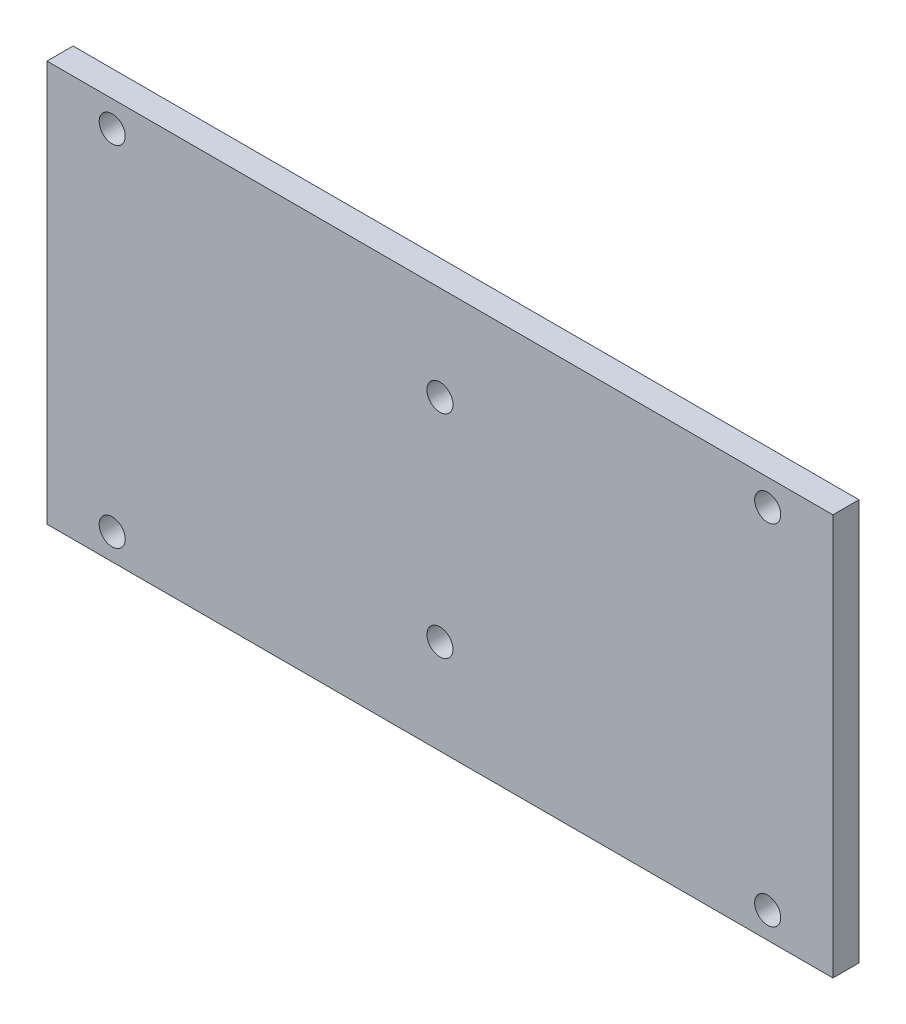
SolidWorks part; units mm, degrees
ref_plane "Alzado" through (0, 0, 0) normal (0, 0, 1) x (1, 0, 0)
ref_plane "Planta" through (0, 0, 0) normal (0, 1, 0) x (1, 0, 0)
ref_plane "Vista lateral" through (0, 0, 0) normal (1, 0, 0) x (0, 0, -1)
sketch "Croquis1" plane through (0, 0, 0) normal (0, 0, 1) x (1, 0, 0)
  line L0 (0, 41.8382) -> (0, -43.7054) construction
  line L1 (60.25, -30.75) -> (-60.25, -30.75)
  line L2 (60.25, -30.75) -> (60.25, 30.75)
  line L3 (60.25, 30.75) -> (-60.25, 30.75)
  line L4 (-60.25, -30.75) -> (-60.25, 30.75)
  line L5 (60.25, -30.75) -> (-60.25, 30.75) construction
  line L6 (60.25, 30.75) -> (-60.25, -30.75) construction
  circle A0 centre (-50.25, 26.75) radius 2
  circle A1 centre (-50.25, -26.75) radius 2
  circle A2 centre (50.25, -26.75) radius 2
  circle A3 centre (50.25, 26.75) radius 2
  circle A4 centre (0, 16.25) radius 2
  circle A5 centre (0, -16.25) radius 2
  point P0 (0, 0)
  dimension "D3" = 4
  dimension "D6" = 4
  dimension "D8" = 4
  dimension "D9" = 4
  dimension "D1" = 120.5
  dimension "D2" = 61.5
  dimension "D4" = 10
  dimension "D5" = 4
  dimension "D7" = 4
  dimension "D10" = 16.25
  dimension "D11" = 16.25
extrude "Saliente-Extruir1" add sketch "Croquis1" along normal blind 4
